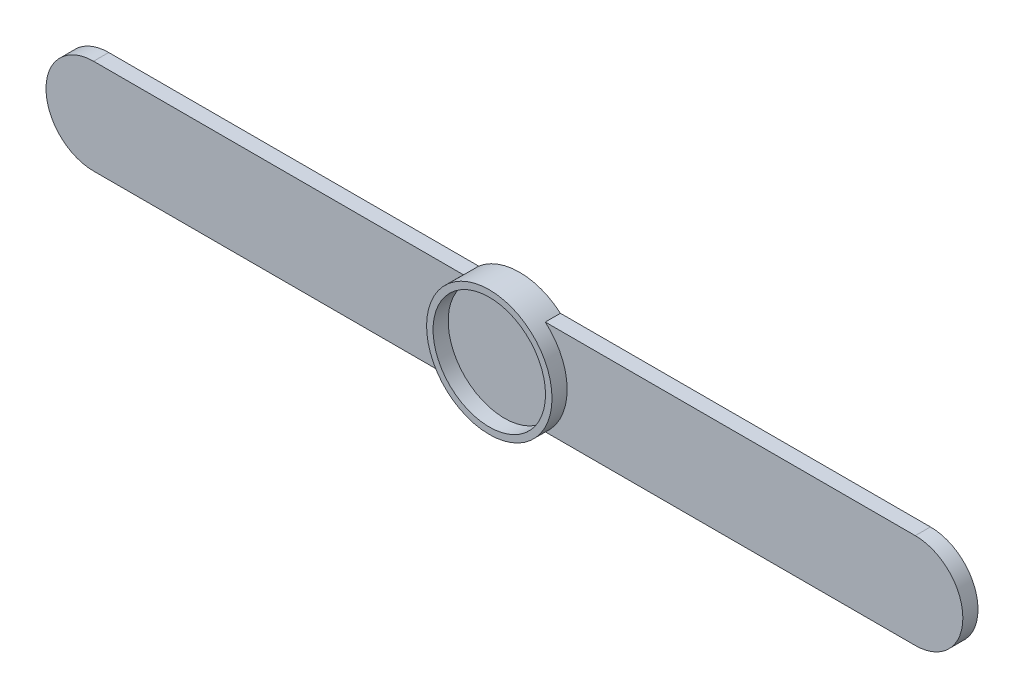
SolidWorks part; units mm, degrees
ref_plane "Спереди" through (0, 0, 0) normal (0, 0, 1) x (1, 0, 0)
ref_plane "Сверху" through (0, 0, 0) normal (0, 1, 0) x (1, 0, 0)
ref_plane "Справа" through (0, 0, 0) normal (1, 0, 0) x (0, 0, -1)
other "Configuration Table"
sketch "Эскиз3" plane through (0, 0, 0) normal (0, 0, 1) x (1, 0, 0)
  line L1 (-95, 11) -> (95, 11)
  line L2 (-95, 11) -> (-95, -11)
  line L3 (-95, -11) -> (95, -11)
  line L4 (95, 11) -> (95, -11)
  line L5 (-95, 11) -> (95, -11) construction
  line L6 (-95, -11) -> (95, 11) construction
  circle A0 centre (0, 0) radius 14.5
  circle A1 centre (-95, 0) radius 11
  circle A2 centre (95, 0) radius 11
  dimension "D1" = 29
  dimension "D2" = 95
  dimension "D3" = 22
extrude "Бобышка-Вытянуть2" add sketch "Эскиз3" along normal blind 3.5 contours L2 A1 | L2 A1 | A1 L3 A0 L1 | L1 A0 L3 | A2 L1 A0 L3 | L4 A2 | L4 A2
sketch "Эскиз5" plane through (0, 0, 3.5) normal (0, 0, 1) x (1, 0, 0)
  circle A0 centre (0, 0) radius 13
  circle A1 centre (0, 0) radius 14.5
  dimension "D1" = 26
extrude "Бобышка-Вытянуть3" add sketch "Эскиз5" along normal blind 3.5
